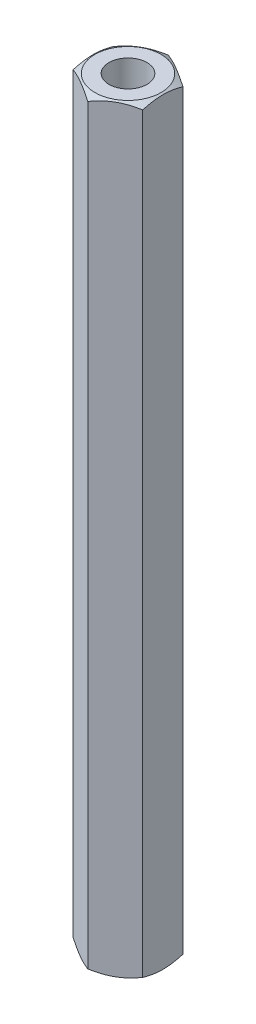
SolidWorks part; units mm, degrees
material "Латунь"
ref_plane "Спереди" through (0, 0, 0) normal (0, 0, 1) x (1, 0, 0)
ref_plane "Сверху" through (0, 0, 0) normal (0, 1, 0) x (1, 0, 0)
ref_plane "Справа" through (0, 0, 0) normal (1, 0, 0) x (0, 0, -1)
sketch "Эскиз1" plane through (0, 0, 0) normal (0, 1, 0) x (1, 0, 0)
  line L1 (0, 3.1754) -> (-2.75, 1.5877)
  line L2 (-2.75, 1.5877) -> (-2.75, -1.5877)
  line L3 (-2.75, -1.5877) -> (0, -3.1754)
  line L4 (0, -3.1754) -> (2.75, -1.5877)
  line L5 (2.75, -1.5877) -> (2.75, 1.5877)
  line L6 (2.75, 1.5877) -> (0, 3.1754)
  circle A0 centre (0, 0) radius 2.75 construction
  circle A1 centre (0, 0) radius 1.5
  dimension "D1" = 3
  dimension "D2" = 5.5
extrude "Бобышка-Вытянуть1" add sketch "Эскиз1" along normal blind 60
sketch "Эскиз3" plane through (0, 0, 0) normal (1, 0, 0) x (0, 0, -1)
  line L0 (0, 0) -> (-2.6125, 0) construction
  line L1 (-2.6125, 0) -> (-8.378, 3.3287)
  line L2 (-8.378, 3.3287) -> (-8.378, 0)
  line L3 (-8.378, 0) -> (-2.6125, 0)
  line L4 (0, 60) -> (-2.6125, 60) construction
  line L5 (-1.5877, 60) -> (1.5877, 60) construction
  line L6 (-3.1754, 60) -> (-1.5877, 60) construction
  line L7 (-2.6125, 60) -> (-11.9319, 54.6195)
  line L8 (-11.9319, 54.6195) -> (-11.9319, 60)
  line L9 (-11.9319, 60) -> (-2.6125, 60)
  line L10 (0, 60) -> (0, 0) construction
  dimension "D1" = 2.6125
  dimension "D2" = 30
  dimension "D3" = 30
revolve "Вырез-Повернуть1" cut sketch "Эскиз3" angle 360 about L10
